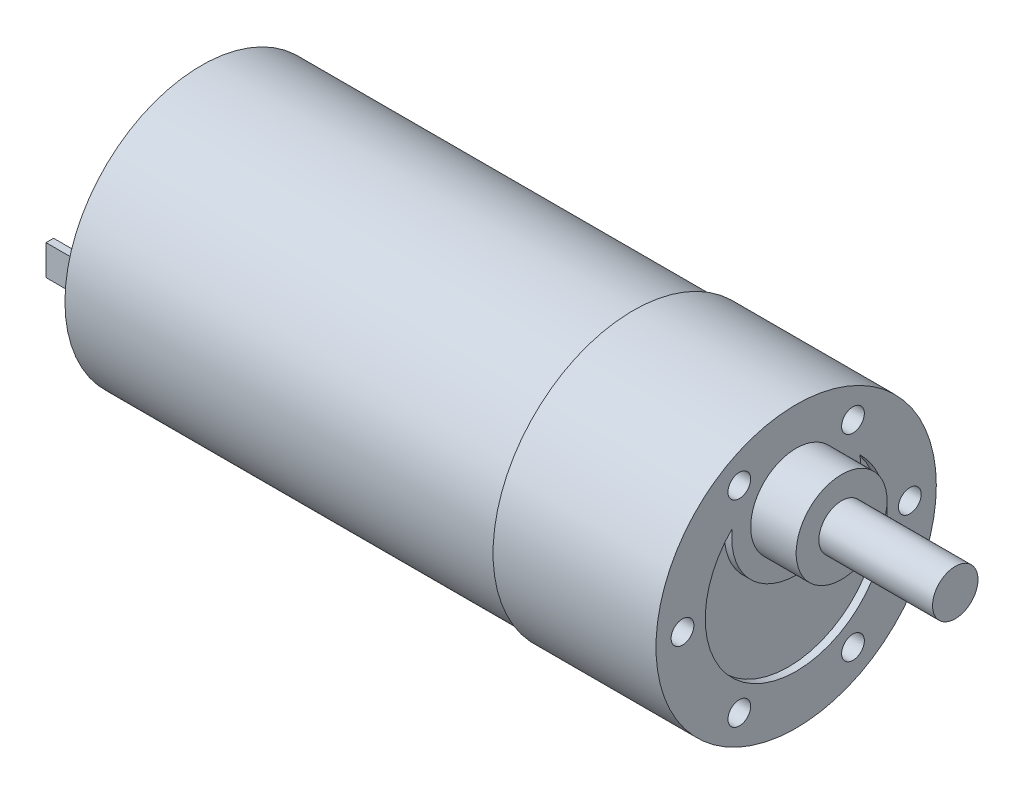
SolidWorks part; units mm, degrees
ref_plane "Front Plane" through (0, 0, 0) normal (0, 0, 1) x (1, 0, 0)
ref_plane "Top Plane" through (0, 0, 0) normal (0, 1, 0) x (1, 0, 0)
ref_plane "Right Plane" through (0, 0, 0) normal (1, 0, 0) x (0, 0, -1)
sketch "Sketch1" plane through (0, 0, 0) normal (1, 0, 0) x (0, 0, -1)
  circle A0 centre (0, 0) radius 18.5
  dimension "D1" = 37
extrude "Boss-Extrude1" add sketch "Sketch1" along normal blind 21.5
sketch "Sketch2" plane through (0, 0, 0) normal (-1, 0, 0) x (0, 0, 1)
  circle A0 centre (0, 0) radius 18
  dimension "D1" = 36
extrude "Boss-Extrude2" add sketch "Sketch2" along normal blind 57
sketch "Sketch3" plane through (-57, 0, 0) normal (-1, 0, 0) x (0, 0, 1)
  line L1 (-14, -2) -> (14, -2)
  line L2 (-14, -2) -> (-14, 2)
  line L3 (-14, 2) -> (14, 2)
  line L4 (14, -2) -> (14, 2)
  line L5 (-14, -2) -> (14, 2) construction
  line L6 (-14, 2) -> (14, -2) construction
  line L7 (-13.5, -2) -> (-14.5, -2)
  line L8 (-13.5, -2) -> (-13.5, 2)
  line L9 (-13.5, 2) -> (-14.5, 2)
  line L10 (-14.5, -2) -> (-14.5, 2)
  line L11 (-13.5, -2) -> (-14.5, 2) construction
  line L12 (-13.5, 2) -> (-14.5, -2) construction
  line L13 (13.5, -2) -> (14.5, -2)
  line L14 (13.5, -2) -> (13.5, 2)
  line L15 (13.5, 2) -> (14.5, 2)
  line L16 (14.5, -2) -> (14.5, 2)
  line L17 (13.5, -2) -> (14.5, 2) construction
  line L18 (13.5, 2) -> (14.5, -2) construction
  point P0 (0, 0)
  point P6 (-14, 0)
  point P11 (14, 0)
  dimension "D1" = 28
  dimension "D2" = 4
  dimension "D3" = 1
  dimension "D4" = 1
extrude "Boss-Extrude3" add sketch "Sketch3" along normal blind 6 contours L8 L9 L10 L7 | L14 L15 L16 L13
sketch "Sketch4" plane through (21.5, 0, 0) normal (1, 0, 0) x (0, 0, -1)
  line L0 (0, 18.5) -> (0, 7.5)
  circle A0 centre (0, 0) radius 18.5 construction
  circle A1 centre (0, 7.5) radius 6
  dimension "D2" = 12
  dimension "D1" = 11
extrude "Boss-Extrude4" add sketch "Sketch4" along normal blind 6
sketch "Sketch5" plane through (27.5, 0, 0) normal (1, 0, 0) x (0, 0, -1)
  circle A0 centre (0, 7.5) radius 3
  dimension "D1" = 6
extrude "Boss-Extrude5" add sketch "Sketch5" along normal blind 15
sketch "Sketch6" plane through (21.5, 0, 0) normal (1, 0, 0) x (0, 0, -1)
  circle A0 centre (0, 0) radius 12
  circle A1 centre (0, 7.5) radius 8.5
  dimension "D1" = 24
  dimension "D2" = 17
extrude "Cut-Extrude1" cut sketch "Sketch6" against normal blind 1 contours A1 A0
sketch "Sketch7" plane through (21.5, 0, 0) normal (1, 0, 0) x (0, 0, -1)
  line L0 (0, 0) -> (-15, 0)
  circle A0 centre (-15, 0) radius 1.5
  circle A1 centre (-7.5, 12.9904) radius 1.5
  circle A2 centre (7.5, 12.9904) radius 1.5
  circle A3 centre (15, 0) radius 1.5
  circle A4 centre (7.5, -12.9904) radius 1.5
  circle A5 centre (-7.5, -12.9904) radius 1.5
  point P16 (0, 0)
  dimension "D2" = 3
  dimension "D1" = 15
  dimension "D3" = 6
extrude "Cut-Extrude2" cut sketch "Sketch7" against normal blind 5 contours A1 | A2 | A3 | A4 | A5 | A0
